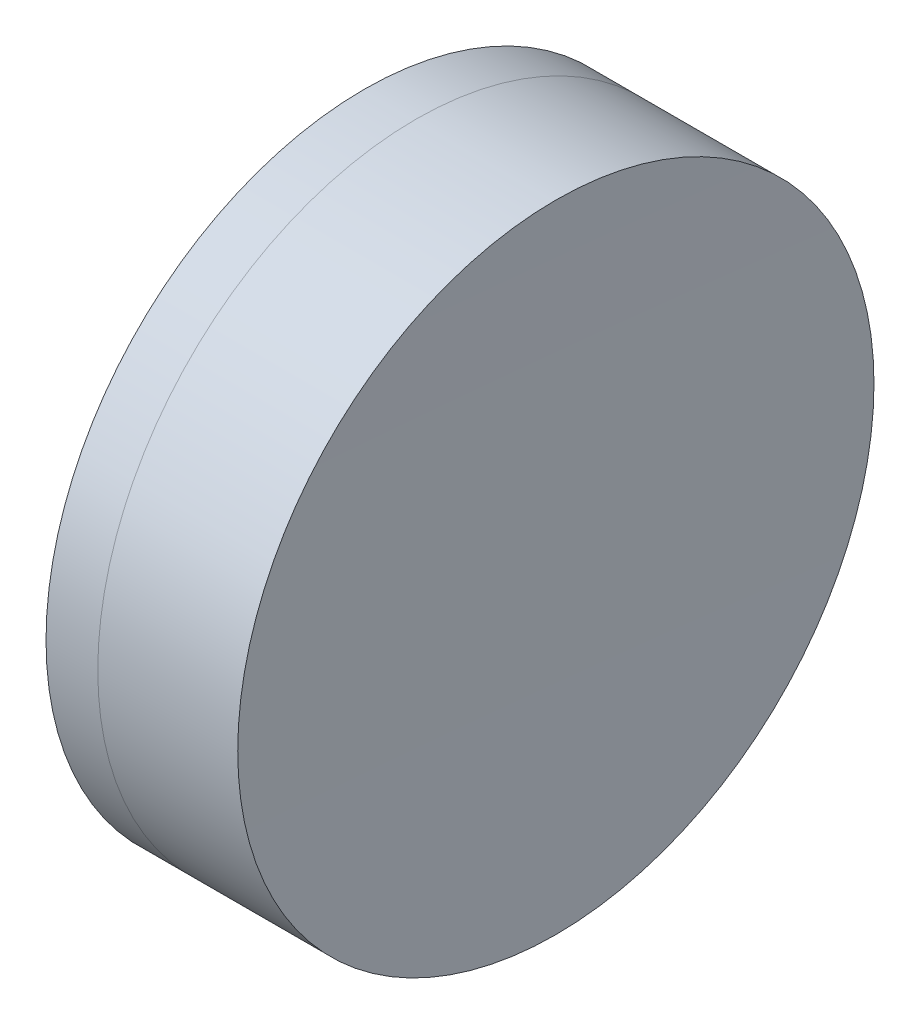
SolidWorks part; units mm, degrees
ref_plane "前视基准面" through (0, 0, 0) normal (0, 0, 1) x (1, 0, 0)
ref_plane "上视基准面" through (0, 0, 0) normal (0, 1, 0) x (1, 0, 0)
ref_plane "右视基准面" through (0, 0, 0) normal (1, 0, 0) x (0, 0, -1)
sketch "草图1" plane through (0, 0, 0) normal (0, 1, 0) x (1, 0, 0)
  line L0 (-0.8161, 0) -> (45.8933, 0) construction
  line L1 (34.7003, -12.7) -> (36.7666, -12.7)
  line L2 (34.7003, 12.7) -> (36.7666, 12.7)
  arc A0 (36.7666, -12.7) -> (36.7666, 12.7) centre (16.804, 0) ccw
  arc A1 (34.7003, 12.7) -> (34.7003, -12.7) centre (53.804, 0) ccw
  point P10 (30.864, 0)
  point P11 (40.464, 0)
  dimension "D3" = 22.94
  dimension "D4" = 23.66
  dimension "D1" = 12.7
  dimension "D2" = 12.7
  dimension "D5" = 9.6
revolve "旋转1" add sketch "草图1" angle 360 about L0
sketch "草图2" plane through (0, 0, 0) normal (0, 1, 0) x (1, 0, 0)
  line L0 (-0.5519, 0) -> (45.4982, 0) construction
  line L2 (36.7666, 12.7) -> (42.3536, 12.7)
  line L3 (36.7666, -12.7) -> (42.3536, -12.7)
  arc A0 (42.3536, 12.7) -> (42.3536, -12.7) centre (942.264, 0) ccw
  arc A1 (36.7666, -12.7) -> (36.7666, 12.7) centre (16.804, 0) ccw construction
  arc A2 (36.7666, -12.7) -> (36.7666, 12.7) centre (16.804, 0) ccw
  point P4 (40.464, 0)
  point P8 (42.264, 0)
  dimension "D1" = 900
  dimension "D2" = 1.8
revolve "旋转2" add sketch "草图2" angle 360 about L0
